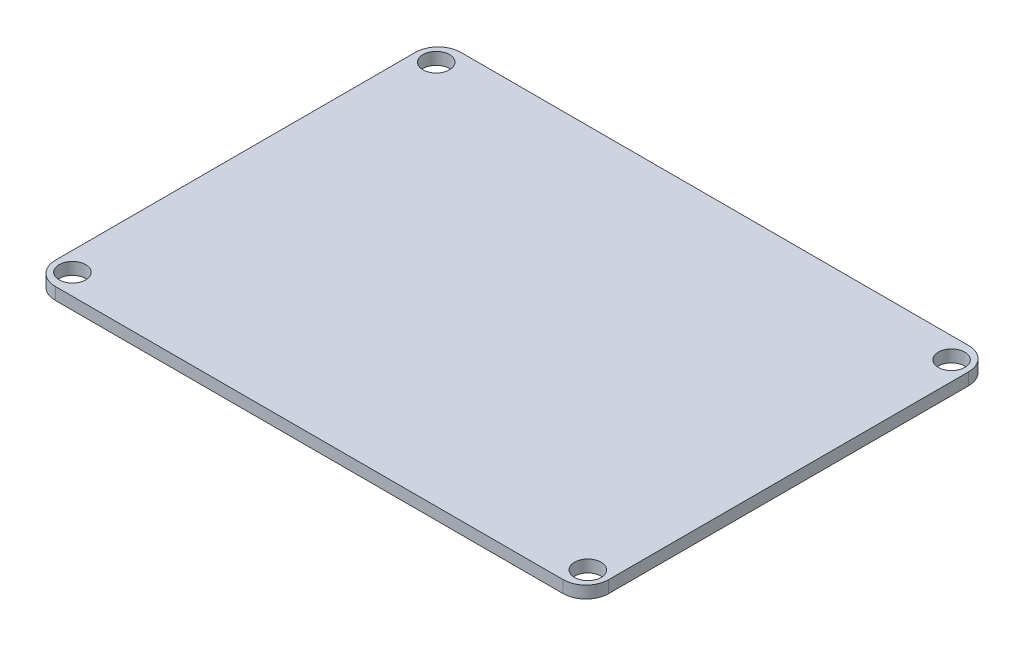
SolidWorks part; units mm, degrees
ref_plane "Front Plane" through (0, 0, 0) normal (0, 0, 1) x (1, 0, 0)
ref_plane "Top Plane" through (0, 0, 0) normal (0, 1, 0) x (1, 0, 0)
ref_plane "Right Plane" through (0, 0, 0) normal (1, 0, 0) x (0, 0, -1)
sketch "Sketch1" plane through (0, 0, 0) normal (0, 1, 0) x (1, 0, 0)
  line L0 (0, -24) -> (0, -26.75) construction
  line L1 (36.5, -26.75) -> (-36.5, -26.75)
  line L2 (36.5, -26.75) -> (36.5, 26.75)
  line L3 (36.5, 26.75) -> (-36.5, 26.75)
  line L4 (-36.5, -26.75) -> (-36.5, 26.75)
  line L5 (36.5, -26.75) -> (-36.5, 26.75) construction
  line L6 (36.5, 26.75) -> (-36.5, -26.75) construction
  line L7 (-34, 24) -> (34, 24) construction
  line L8 (-34, 24) -> (-34, -24) construction
  line L9 (-34, -24) -> (34, -24) construction
  line L10 (34, 24) -> (34, -24) construction
  line L11 (-36.5, 0) -> (-34, 0) construction
  circle A0 centre (-34, 24) radius 1.75
  circle A1 centre (34, 24) radius 1.75
  circle A2 centre (34, -24) radius 1.75
  circle A3 centre (-34, -24) radius 1.75
  point P0 (0, 0)
  dimension "D3" = 3.5
  dimension "D1" = 73
  dimension "D2" = 53.5
  dimension "D4" = 68
  dimension "D5" = 48
extrude "Boss-Extrude1" add sketch "Sketch1" along normal blind 1.6
fillet "Fillet1" radius 3 4 edges at (-36.5, 0.8, -26.75) (36.5, 0.8, -26.75) (36.5, 0.8, 26.75) (-36.5, 0.8, 26.75)
